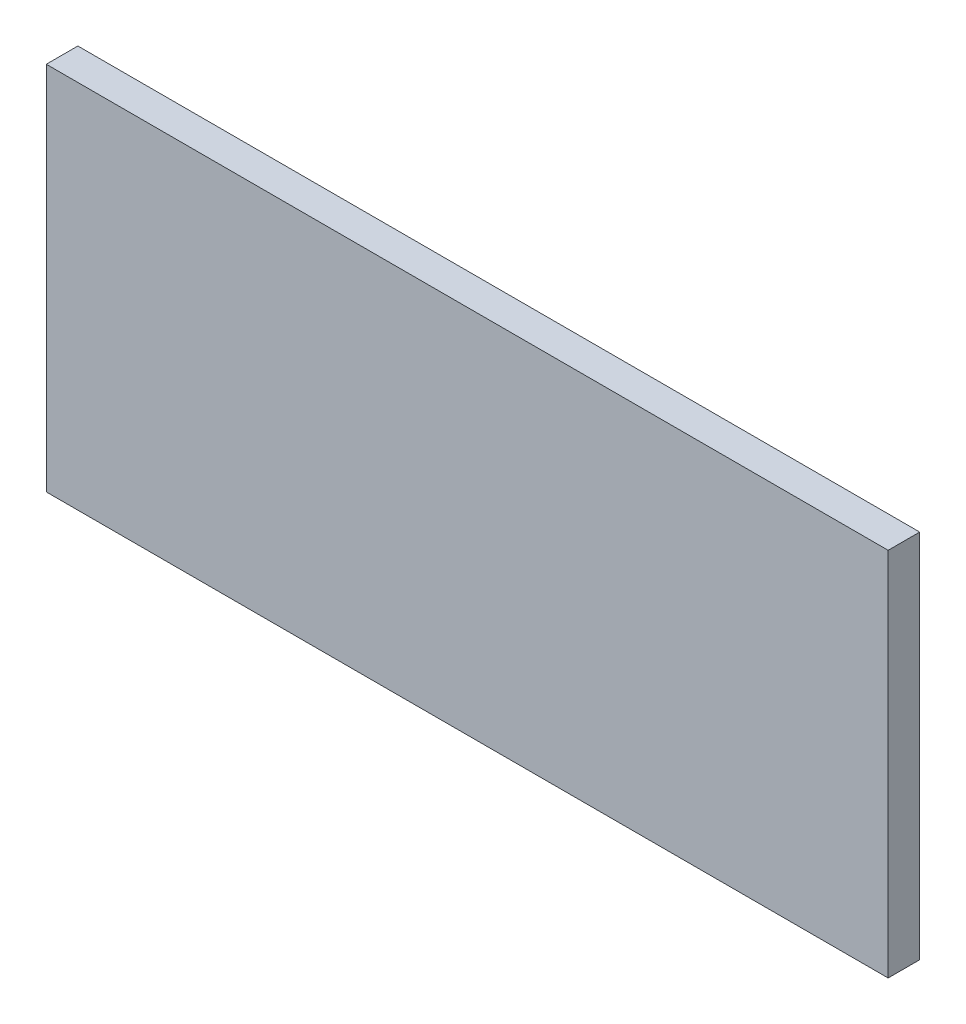
SolidWorks part; units mm, degrees
material "Oak"
ref_plane "Front Plane" through (0, 0, 0) normal (0, 0, 1) x (1, 0, 0)
ref_plane "Top Plane" through (0, 0, 0) normal (0, 1, 0) x (1, 0, 0)
ref_plane "Right Plane" through (0, 0, 0) normal (1, 0, 0) x (0, 0, -1)
sketch "Sketch1" plane through (0, 0, 0) normal (0, 0, 1) x (1, 0, 0)
  line L0 (-200, -75.5) -> (-200, -85.5)
  line L1 (-200, -75.5) -> (200, -75.5) construction
  line L2 (-200, -75.5) -> (-200, 75.5)
  line L3 (-200, 75.5) -> (200, 75.5)
  line L4 (200, -75.5) -> (200, 75.5)
  line L5 (-200, -75.5) -> (200, 75.5) construction
  line L6 (-200, 75.5) -> (200, -75.5) construction
  line L7 (-200, -85.5) -> (200, -85.5)
  line L8 (200, -85.5) -> (200, -75.5)
  point P0 (0, 0)
  dimension "D1" = 151
  dimension "D2" = 400
  dimension "D3" = 10
extrude "Boss-Extrude1" add sketch "Sketch1" along normal blind 15
sketch "Sketch2" plane through (0, 0, 0) normal (0, 0, -1) x (-1, 0, 0)
  line L0 (0, 7.7) -> (0, -7.7) construction
  line L3 (-170, 75.5) -> (-170, -85.5) construction
  line L4 (-200, 75.5) -> (200, 75.5) construction
  line L5 (200, -85.5) -> (-200, -85.5) construction
  line L6 (170, -60.5) -> (-170, -60.5) construction
  line L7 (-170, -85.5) -> (-170, -60.5) construction
  line L8 (-170, -75.5) -> (170, -75.5) construction
  line L10 (-200, -85.5) -> (-200, 75.5) construction
  line L11 (170, 75.5) -> (170, -85.5) construction
  line L12 (-170, -60.5) -> (-170, -75.5) construction
  line L13 (-170, -68) -> (-146, -68) construction
  line L14 (142, -60.5) -> (142, -75.5) construction
  circle A1 centre (-142, -68) radius 4
  dimension "D3" = 10
  dimension "D6" = 8
  dimension "D1" = 30
  dimension "D2" = 15
  dimension "D4" = 28
  dimension "D5" = 24
extrude "Cut-Extrude1" cut sketch "Sketch2" against normal blind 10
pattern_linear "LPattern1" count 3 spacing 142 along (-1, 0, 0) of "Cut-Extrude1"
sketch "Sketch3" plane through (0, 0, 0) normal (0, 0, -1) x (-1, 0, 0)
  line L0 (-200, -60.5) -> (200, -60.5) construction
  line L1 (-200, -85.5) -> (-200, 75.5) construction
  line L2 (200, 75.5) -> (200, -85.5) construction
  line L3 (200, -85.5) -> (-200, -85.5) construction
  line L4 (-157, 75.5) -> (-157, -60.5) construction
  line L5 (-200, 75.5) -> (200, 75.5) construction
  line L6 (-157, 75.5) -> (-172, 75.5) construction
  line L7 (-164.5, 75.5) -> (-164.5, 64.5) construction
  line L8 (-172, -45.5) -> (-157, -45.5) construction
  line L9 (-172, 75.5) -> (-172, -60.5) construction
  circle A0 centre (-164.5, 60.5) radius 4
  dimension "D2" = 15
  dimension "D5" = 8
  dimension "D1" = 25
  dimension "D3" = 15
  dimension "D4" = 11
  dimension "D6" = 28
extrude "Cut-Extrude2" cut sketch "Sketch3" against normal blind 10
pattern_linear "LPattern2" count 2 spacing 106 along (0, -1, 0) of "Cut-Extrude2"
mirror "Mirror1" about plane through (0, 0, 0) normal (1, 0, 0) of "LPattern2", "Cut-Extrude2"
sketch "Sketch4" plane through (0, 0, 0) normal (0, 0, 1) x (1, 0, 0)
  line L0 (-200, -85.5) -> (-200, -100.5)
  line L1 (-200, -100.5) -> (200, -100.5)
  line L2 (200, -100.5) -> (200, -85.5)
  line L3 (-200, -85.5) -> (200, -85.5)
  dimension "D1" = 15
extrude "Boss-Extrude2" add sketch "Sketch4" along normal blind 15
equation "\"A\"= 400mm"
equation "\"B\"= 151mm"
equation "\"C\"= 15mm"
equation "\"D\"= 10mm"
equation "\"D1@Sketch1\"=\"B\""
equation "\"D2@Sketch1\"=\"A\""
equation "\"D3@Sketch1\"=\"D\""
equation "\"D1@Boss-Extrude1\"=\"C\""
equation "\"D1@Sketch2\"=\"C\"*2"
equation "\"D2@Sketch2\"=\"C\""
equation "\"D2@Sketch3\"=\"C\""
equation "\"D3@Sketch2\"=\"D\""
equation "\"D1@Sketch3\"=\"D\"+\"C\""
equation "\"D6@Sketch3\"=\"C\"+13mm"
equation "\"D5@Sketch2\"=11mm+13mm"
equation "\"D4@Sketch2\"=15mm+13mm"
equation "\"D1@Sketch4\"=\"C\""
equation "\"D1@Boss-Extrude2\"=\"C\""
